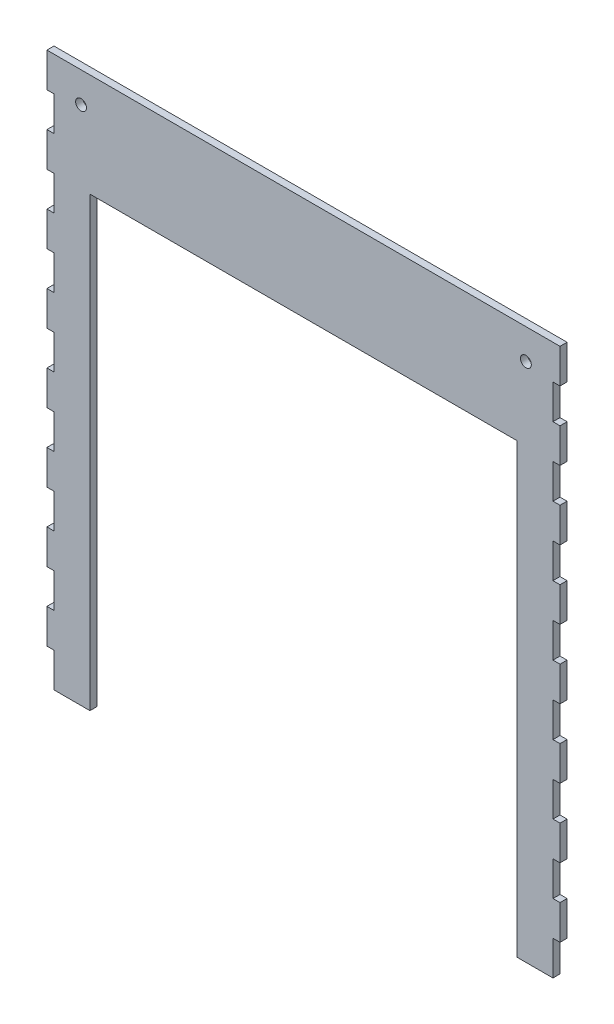
SolidWorks part; units mm, degrees
ref_plane "Front Plane" through (0, 0, 0) normal (0, 0, 1) x (1, 0, 0)
ref_plane "Top Plane" through (0, 0, 0) normal (0, 1, 0) x (1, 0, 0)
ref_plane "Right Plane" through (0, 0, 0) normal (1, 0, 0) x (0, 0, -1)
sketch "Sketch1" plane through (0, 0, 0) normal (0, 0, 1) x (1, 0, 0)
  line L0 (184.15, 0) -> (184.15, 406.4) construction
  line L1 (-189.357, 0) -> (189.357, 0)
  line L2 (-189.357, 0) -> (-189.357, 406.4)
  line L3 (-189.357, 406.4) -> (189.357, 406.4)
  line L4 (189.357, 0) -> (189.357, 406.4)
  line L5 (-157.607, 0) -> (157.607, 0)
  line L6 (-157.607, 0) -> (-157.607, 330.2)
  line L7 (-157.607, 330.2) -> (157.607, 330.2)
  line L8 (157.607, 0) -> (157.607, 330.2)
  line L9 (189.357, 0) -> (184.15, 0)
  line L10 (189.357, 0) -> (189.357, 25.4)
  line L11 (189.357, 25.4) -> (184.15, 25.4)
  line L12 (184.15, 0) -> (184.15, 25.4)
  line L13 (-184.15, 0) -> (-184.15, 406.4) construction
  line L14 (-184.15, 0) -> (-184.15, 25.4)
  line L15 (-184.15, 0) -> (-189.357, 0)
  line L16 (-189.357, 0) -> (-189.357, 25.4)
  line L17 (-184.15, 25.4) -> (-189.357, 25.4)
  line L18 (-184.15, 50.8) -> (-184.15, 76.2)
  line L19 (-184.15, 50.8) -> (-189.357, 50.8)
  line L20 (-189.357, 50.8) -> (-189.357, 76.2)
  line L21 (-184.15, 76.2) -> (-189.357, 76.2)
  line L22 (-184.15, 101.6) -> (-184.15, 127)
  line L23 (-184.15, 101.6) -> (-189.357, 101.6)
  line L24 (-189.357, 101.6) -> (-189.357, 127)
  line L25 (-184.15, 127) -> (-189.357, 127)
  line L26 (-184.15, 152.4) -> (-184.15, 177.8)
  line L27 (-184.15, 152.4) -> (-189.357, 152.4)
  line L28 (-189.357, 152.4) -> (-189.357, 177.8)
  line L29 (-184.15, 177.8) -> (-189.357, 177.8)
  line L30 (-184.15, 203.2) -> (-184.15, 228.6)
  line L31 (-184.15, 203.2) -> (-189.357, 203.2)
  line L32 (-189.357, 203.2) -> (-189.357, 228.6)
  line L33 (-184.15, 228.6) -> (-189.357, 228.6)
  line L34 (-184.15, 254) -> (-184.15, 279.4)
  line L35 (-184.15, 254) -> (-189.357, 254)
  line L36 (-189.357, 254) -> (-189.357, 279.4)
  line L37 (-184.15, 279.4) -> (-189.357, 279.4)
  line L38 (-184.15, 304.8) -> (-184.15, 330.2)
  line L39 (-184.15, 304.8) -> (-189.357, 304.8)
  line L40 (-189.357, 304.8) -> (-189.357, 330.2)
  line L41 (-184.15, 330.2) -> (-189.357, 330.2)
  line L42 (-184.15, 355.6) -> (-184.15, 381)
  line L43 (-184.15, 355.6) -> (-189.357, 355.6)
  line L44 (-189.357, 355.6) -> (-189.357, 381)
  line L45 (-184.15, 381) -> (-189.357, 381)
  line L46 (189.357, 50.8) -> (189.357, 76.2)
  line L47 (189.357, 50.8) -> (184.15, 50.8)
  line L48 (184.15, 50.8) -> (184.15, 76.2)
  line L49 (189.357, 76.2) -> (184.15, 76.2)
  line L50 (189.357, 101.6) -> (189.357, 127)
  line L51 (189.357, 101.6) -> (184.15, 101.6)
  line L52 (184.15, 101.6) -> (184.15, 127)
  line L53 (189.357, 127) -> (184.15, 127)
  line L54 (189.357, 152.4) -> (189.357, 177.8)
  line L55 (189.357, 152.4) -> (184.15, 152.4)
  line L56 (184.15, 152.4) -> (184.15, 177.8)
  line L57 (189.357, 177.8) -> (184.15, 177.8)
  line L58 (189.357, 203.2) -> (189.357, 228.6)
  line L59 (189.357, 203.2) -> (184.15, 203.2)
  line L60 (184.15, 203.2) -> (184.15, 228.6)
  line L61 (189.357, 228.6) -> (184.15, 228.6)
  line L62 (189.357, 254) -> (189.357, 279.4)
  line L63 (189.357, 254) -> (184.15, 254)
  line L64 (184.15, 254) -> (184.15, 279.4)
  line L65 (189.357, 279.4) -> (184.15, 279.4)
  line L66 (189.357, 304.8) -> (189.357, 330.2)
  line L67 (189.357, 304.8) -> (184.15, 304.8)
  line L68 (184.15, 304.8) -> (184.15, 330.2)
  line L69 (189.357, 330.2) -> (184.15, 330.2)
  line L70 (189.357, 355.6) -> (189.357, 381)
  line L71 (189.357, 355.6) -> (184.15, 355.6)
  line L72 (184.15, 355.6) -> (184.15, 381)
  line L73 (189.357, 381) -> (184.15, 381)
  circle A0 centre (-164.15, 384.05) radius 4
  circle A1 centre (164.15, 384.05) radius 4
  point P4 (0, 0)
  point P10 (0, 330.2)
  dimension "D2" = 8
  dimension "D1" = 378.714
  dimension "12" = 406.4
  dimension "D3" = 22.35
  dimension "D4" = 25.207
  dimension "D5" = 25.207
  dimension "D6" = 76.2
  dimension "D7" = 31.75
  dimension "D8" = 5.207
  dimension "D9" = 5.207
  dimension "D10" = 25.4
  dimension "D13" = 25.4
  dimension "D11" = 2
  dimension "D12" = 8
extrude "Boss-Extrude1" add sketch "Sketch1" along normal blind 5.207 contours L8 L1 L4 L3 L2 L6 L7 A1 A0
